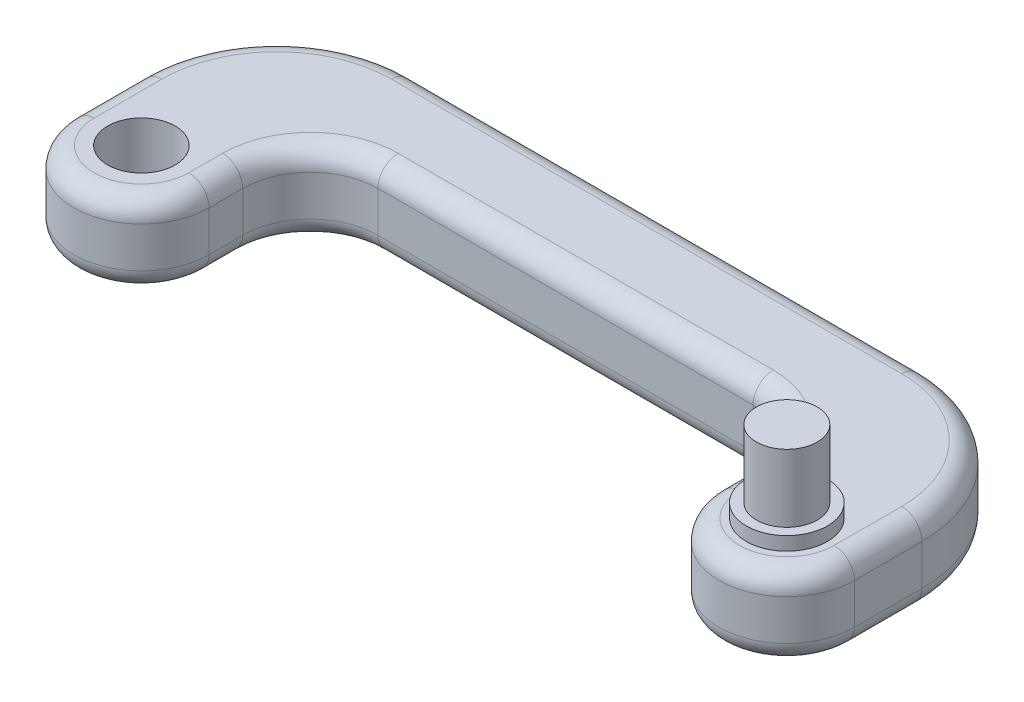
SolidWorks part; units mm, degrees
ref_plane "Front Plane" through (0, 0, 0) normal (0, 0, 1) x (1, 0, 0)
ref_plane "Top Plane" through (0, 0, 0) normal (0, 1, 0) x (1, 0, 0)
ref_plane "Right Plane" through (0, 0, 0) normal (1, 0, 0) x (0, 0, -1)
sketch "Sketch7" plane through (0, 0, 0) normal (0, 1, 0) x (1, 0, 0)
  line L2 (-105.5, 0) -> (-105.5, 30)
  line L3 (-85.5, 0) -> (-85.5, 15)
  line L4 (-105.5, 30) -> (-85.5, 30)
  line L6 (-85.5, 30) -> (10, 30)
  line L7 (-85.5, 15) -> (-10, 15)
  line L10 (10, 0) -> (10, 30.0013)
  line L11 (-10, 0) -> (-10, 15)
  line L12 (10, 30.0013) -> (-10, 30.0013)
  line L13 (-10, 30) -> (-10, 30.0013)
  arc A0 (-10, 0) -> (10, 0) centre (0, 0) ccw
  arc A1 (-105.5, 0) -> (-85.5, 0) centre (-95.5, 0) ccw
  circle A2 centre (-95.5, 0) radius 5
extrude "Boss-Extrude5" add sketch "Sketch7" along normal blind 12 contours L2 A1 L3 L7 L11 A0 L10 L6 L4 A2
sketch "Sketch8" plane through (0, 12, 0) normal (0, 1, 0) x (1, 0, 0)
  circle A0 centre (0, 0) radius 6
extrude "Boss-Extrude6" add sketch "Sketch8" along normal blind 2 contours A0
sketch "Sketch9" plane through (0, 14, 0) normal (0, 1, 0) x (1, 0, 0)
  circle A0 centre (0, 0) radius 4.5
extrude "Boss-Extrude7" add sketch "Sketch9" along normal blind 10
fillet "Fillet2" radius 20 2 edges at (10, 6, -30) (-105.5, 6, -30)
fillet "Fillet3" radius 10 2 edges at (-10, 6, -15) (-85.5, 6, -15)
fillet "Fillet5" radius 3 24 edges at (-47.75, 12, -30) (4.1421, 12, -24.1421) (10, 12, -5) (0, 12, 10) (-10, 12, -2.5) (-12.9289, 12, -12.0711) (-47.75, 12, -15) (-82.5711, 12, -12.0711) (-85.5, 12, -2.5) (-95.5, 12, 10) (-105.5, 12, -5) (-105.5, 0, -5) (-95.5, 0, 10) (-85.5, 0, -2.5) (-82.5711, 0, -12.0711) (-47.75, 0, -15) (-12.9289, 0, -12.0711) (-10, 0, -2.5) (0, 0, 10) (10, 0, -5) (4.1421, 0, -24.1421) (-47.75, 0, -30) (-99.6421, 12, -24.1421) (-99.6421, 0, -24.1421)
